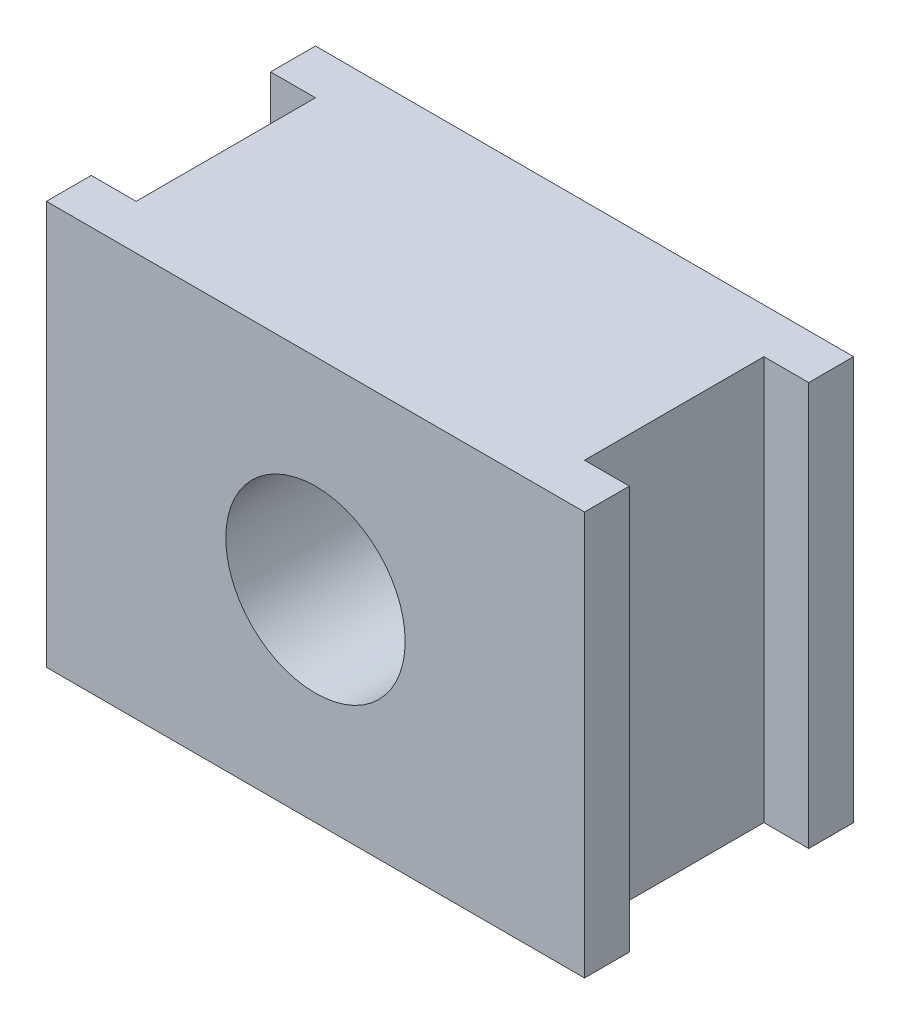
SolidWorks part; units mm, degrees
ref_plane "前视基准面" through (0, 0, 0) normal (0, 0, 1) x (1, 0, 0)
ref_plane "上视基准面" through (0, 0, 0) normal (0, 1, 0) x (1, 0, 0)
ref_plane "右视基准面" through (0, 0, 0) normal (1, 0, 0) x (0, 0, -1)
sketch "草图1" plane through (0, 0, 0) normal (0, 0, 1) x (1, 0, 0)
  line L1 (-30, 22.5) -> (30, 22.5)
  line L2 (-30, 22.5) -> (-30, -22.5)
  line L3 (-30, -22.5) -> (30, -22.5)
  line L4 (30, 22.5) -> (30, -22.5)
  line L5 (-30, 22.5) -> (30, -22.5) construction
  line L6 (-30, -22.5) -> (30, 22.5) construction
  point P0 (0, 0)
  dimension "D1" = 60
  dimension "D2" = 45
extrude "凸台-拉伸1" add sketch "草图1" along normal blind 30
sketch "草图2" plane through (0, 22.5, 0) normal (0, 1, 0) x (1, 0, 0)
  line L0 (30, -15) -> (-42.2839, -15) construction
  line L1 (-40, -5) -> (-25, -5)
  line L2 (-40, -5) -> (-40, -25)
  line L3 (-40, -25) -> (-25, -25)
  line L4 (-25, -5) -> (-25, -25)
  line L5 (-40, -5) -> (-25, -25) construction
  line L6 (-40, -25) -> (-25, -5) construction
  line L7 (30, -30) -> (30, 0) construction
  line L8 (-30, -30) -> (-30, 0) construction
  line L9 (0, 0) -> (0, -42.6762) construction
  line L10 (40, -25) -> (25, -5) construction
  line L11 (40, -5) -> (25, -25) construction
  line L12 (25, -5) -> (25, -25)
  line L13 (40, -25) -> (25, -25)
  line L14 (40, -5) -> (40, -25)
  line L15 (40, -5) -> (25, -5)
  point P0 (-32.5, -15)
  point P18 (32.5, -15)
  dimension "D1" = 20
  dimension "D2" = 5
  dimension "D3" = 15
extrude "切除-拉伸1" cut sketch "草图2" against normal blind 80
sketch "草图3" plane through (0, 0, 30) normal (0, 0, 1) x (1, 0, 0)
  circle A0 centre (0, 0) radius 10
  dimension "D1" = 20
extrude "切除-拉伸2" cut sketch "草图3" against normal blind 80
